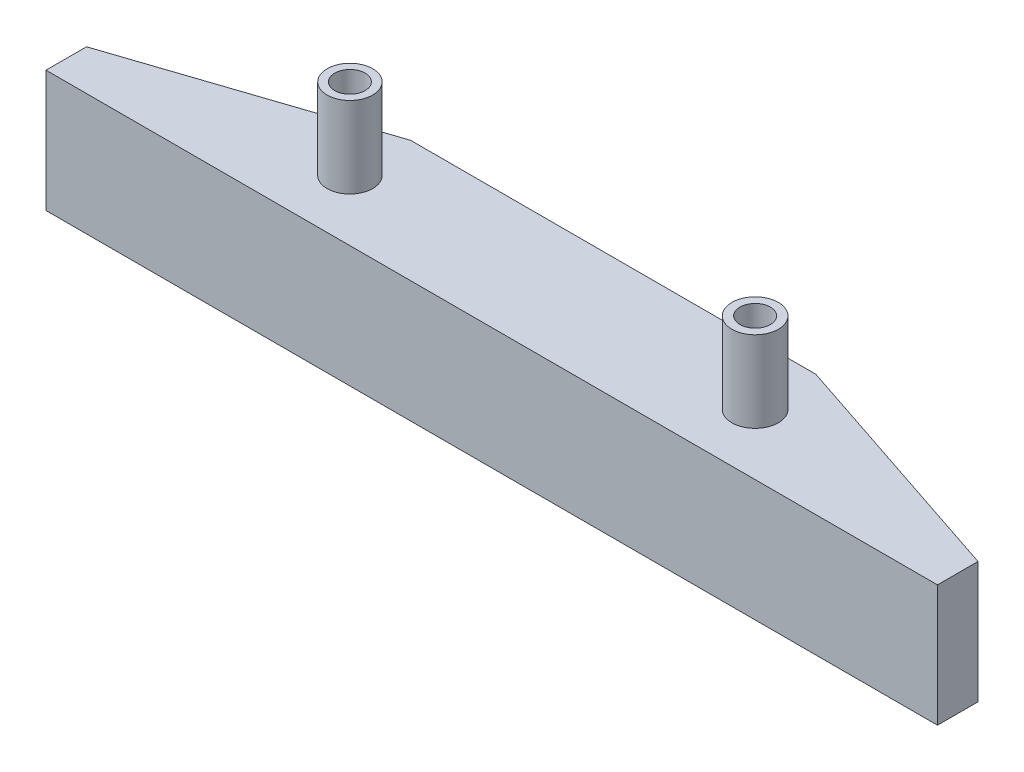
SolidWorks part; units mm, degrees
ref_plane "Front Plane" through (0, 0, 0) normal (0, 0, 1) x (1, 0, 0)
ref_plane "Top Plane" through (0, 0, 0) normal (0, 1, 0) x (1, 0, 0)
ref_plane "Right Plane" through (0, 0, 0) normal (1, 0, 0) x (0, 0, -1)
sketch "Sketch1" plane through (0, 0, 0) normal (0, 1, 0) x (1, 0, 0)
  line L0 (0, 0) -> (88, 0)
  line L1 (88, 0) -> (88, 4)
  line L2 (88, 4) -> (64, 12)
  line L3 (64, 12) -> (24, 12)
  line L4 (24, 12) -> (0, 4)
  line L5 (0, 4) -> (0, 0)
  point P3 (44, 12)
  point P8 (44, 0)
  dimension "D1" = 88
  dimension "D2" = 4
  dimension "D3" = 12
  dimension "D4" = 40
extrude "Boss-Extrude1" add sketch "Sketch1" along normal blind 12
sketch "Sketch2" plane through (0, 0, 0) normal (0, -1, 0) x (-1, 0, 0)
  line L0 (-44, 12) -> (-44, 0) construction
  line L1 (-64, 12) -> (-24, 12) construction
  line L2 (0, 0) -> (-88, 0) construction
  circle A0 centre (-24, 6) radius 2.5
  circle A1 centre (-64, 6) radius 2.5
  point P13 (-44, 6)
  dimension "D1" = 5
extrude "Cut-Extrude1" cut sketch "Sketch2" against normal blind 5
sketch "Sketch3" plane through (0, 5, 0) normal (0, -1, 0) x (-1, 0, 0)
  circle A0 centre (-24, 6) radius 1.5
  circle A1 centre (-64, 6) radius 1.5
  dimension "D1" = 3
extrude "Cut-Extrude2" cut sketch "Sketch3" against normal through all
sketch "Sketch4" plane through (0, 12, 0) normal (0, 1, 0) x (1, 0, 0)
  circle A0 centre (24, 6) radius 1.5
  circle A1 centre (24, 6) radius 2.25
  circle A2 centre (64, 6) radius 2.2946
  circle A3 centre (64, 6) radius 2.25
  circle A4 centre (64, 6) radius 1.5 construction
  circle A5 centre (64, 6) radius 1.5
  dimension "D2" = 4.5
extrude "Boss-Extrude2" add sketch "Sketch4" along normal blind 8 contours A0 | A1 | A5 | A2
